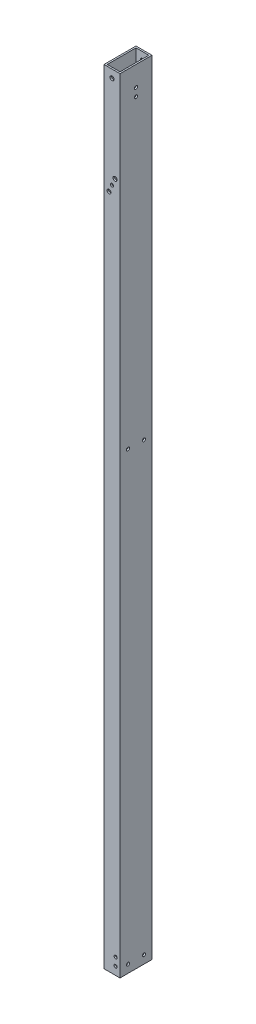
SolidWorks part; units mm, degrees
material "6061-T6 (SS)"
ref_plane "Front Plane" through (0, 0, 0) normal (0, 0, 1) x (1, 0, 0)
ref_plane "Top Plane" through (0, 0, 0) normal (0, 1, 0) x (1, 0, 0)
ref_plane "Right Plane" through (0, 0, 0) normal (1, 0, 0) x (0, 0, -1)
sketch "Sketch1" plane through (0, 0, 0) normal (0, 1, 0) x (1, 0, 0)
  line L1 (0, 0) -> (25.4, 0)
  line L2 (0, 0) -> (0, 50.8)
  line L3 (0, 50.8) -> (25.4, 50.8)
  line L4 (25.4, 0) -> (25.4, 50.8)
  dimension "D1" = 25.4
  dimension "D2" = 50.8
extrude "Extrude-Thin1" add sketch "Sketch1" along normal blind 1244.6 thin thin type one direction reverse wall 2.54
sketch "Sketch3" plane through (25.4, 0, 0) normal (1, 0, 0) x (0, 0, -1)
  circle A0 centre (12.7, 12.7) radius 2.4892 construction
  circle A1 centre (38.1, 12.9602) radius 2.4892 construction
  circle A2 centre (12.7, 721.6321) radius 2.5019 construction
  circle A3 centre (38.1, 721.6321) radius 2.5019 construction
  circle A9 centre (12.7, 12.7) radius 2.4892
  circle A10 centre (38.1, 12.9602) radius 2.4892
  circle A11 centre (12.7, 721.6321) radius 2.5019
  circle A12 centre (38.1, 721.6321) radius 2.5019
extrude "Cut-Extrude1" cut sketch "Sketch3" against normal through all
sketch "Sketch4" plane through (0, 0, 0) normal (-1, 0, 0) x (0, 0, 1)
  circle A0 centre (-25.4, 1200.15) radius 2.4892 construction
  circle A1 centre (-25.4, 1212.85) radius 2.4892 construction
  circle A2 centre (-25.4, 1200.15) radius 2.4892
  circle A3 centre (-25.4, 1212.85) radius 2.4892
extrude "Cut-Extrude2" cut sketch "Sketch4" against normal through all
sketch "Sketch8" plane through (0, 0, -50.8) normal (0, 0, -1) x (-1, 0, 0)
  line L0 (-25.4, 1244.6) -> (-25.4, 0) construction
  line L1 (-25.4, 1244.6) -> (0, 1244.6) construction
  circle A0 centre (-12.7, 1084.8046) radius 2.4892
  dimension "D1" = 12.7
  dimension "D2" = 4.9784
  dimension "D3" = 159.7954
extrude "Cut-Extrude4" cut sketch "Sketch8" against normal through all
sketch "Sketch10" plane through (25.4, 0, 0) normal (1, 0, 0) x (0, 0, -1)
  line L0 (38.1, 1231.9) -> (38.1, 1219.2) construction
  line L1 (38.1, 1219.2) -> (38.1, 1206.5) construction
  line L2 (38.1, 1206.5) -> (38.1, 1193.8) construction
  line L3 (0, 1244.6) -> (50.8, 1244.6) construction
  line L4 (50.8, 1244.6) -> (50.8, 0) construction
  circle A0 centre (38.1, 1231.9) radius 2.4892
  circle A1 centre (38.1, 1219.2) radius 2.4892
  circle A2 centre (38.1, 1206.5) radius 2.4892
  circle A3 centre (38.1, 1193.8) radius 2.4892
  dimension "D1" = 12.7
  dimension "D4" = 4.9784
  dimension "D2" = 12.7
  dimension "D3" = 12.7
extrude "Cut-Extrude5" [suppressed] cut sketch "Sketch10" against normal through all
sketch "Sketch11" plane through (0, 0, 0) normal (0, 0, 1) x (1, 0, 0)
  circle A0 centre (18.415, 12.7) radius 2.4892 construction
  circle A1 centre (18.415, 25.4) radius 2.4892 construction
  circle A2 centre (18.415, 12.7) radius 2.4892
  circle A3 centre (18.415, 25.4) radius 2.4892
extrude "Cut-Extrude6" cut sketch "Sketch11" against normal through all
sketch "Sketch12" plane through (0, 0, -50.8) normal (0, 0, -1) x (-1, 0, 0)
  line L0 (0, 1244.6) -> (0, 0) construction
  line L1 (-25.4, 1244.6) -> (0, 1244.6) construction
  circle A0 centre (-12.7, 1231.9) radius 3.175
  dimension "D1" = 6.35
  dimension "D2" = 12.7
  dimension "D3" = 12.7
extrude "Cut-Extrude7" cut sketch "Sketch12" against normal through all
sketch "Sketch13" plane through (0, 0, -50.8) normal (0, 0, -1) x (-1, 0, 0)
  line L0 (-17.4625, 1095.9171) -> (-7.9375, 1073.6921) construction
  line L1 (-25.4, 1103.8546) -> (0, 1103.8546) construction
  line L2 (-25.4, 1244.6) -> (-25.4, 0) construction
  line L3 (0, 1244.6) -> (0, 0) construction
  line L4 (-25.4, 1065.7546) -> (0, 1065.7546) construction
  circle A0 centre (-17.4625, 1095.9171) radius 3.175
  circle A1 centre (-7.9375, 1073.6921) radius 3.175
  circle A2 centre (-12.7, 1084.8046) radius 2.4892 construction
  circle A3 centre (-12.7, 1084.8046) radius 2.4892 construction
  dimension "D1" = 6.35
  dimension "D2" = 38.1
  dimension "D3" = 7.9375
  dimension "D4" = 7.9375
  dimension "D5" = 7.9375
  dimension "D6" = 7.9375
extrude "Cut-Extrude8" cut sketch "Sketch13" against normal through all
equation "\"D4@Sketch13\"=\"D3@Sketch13\""
equation "\"D5@Sketch13\"=0.3125in"
